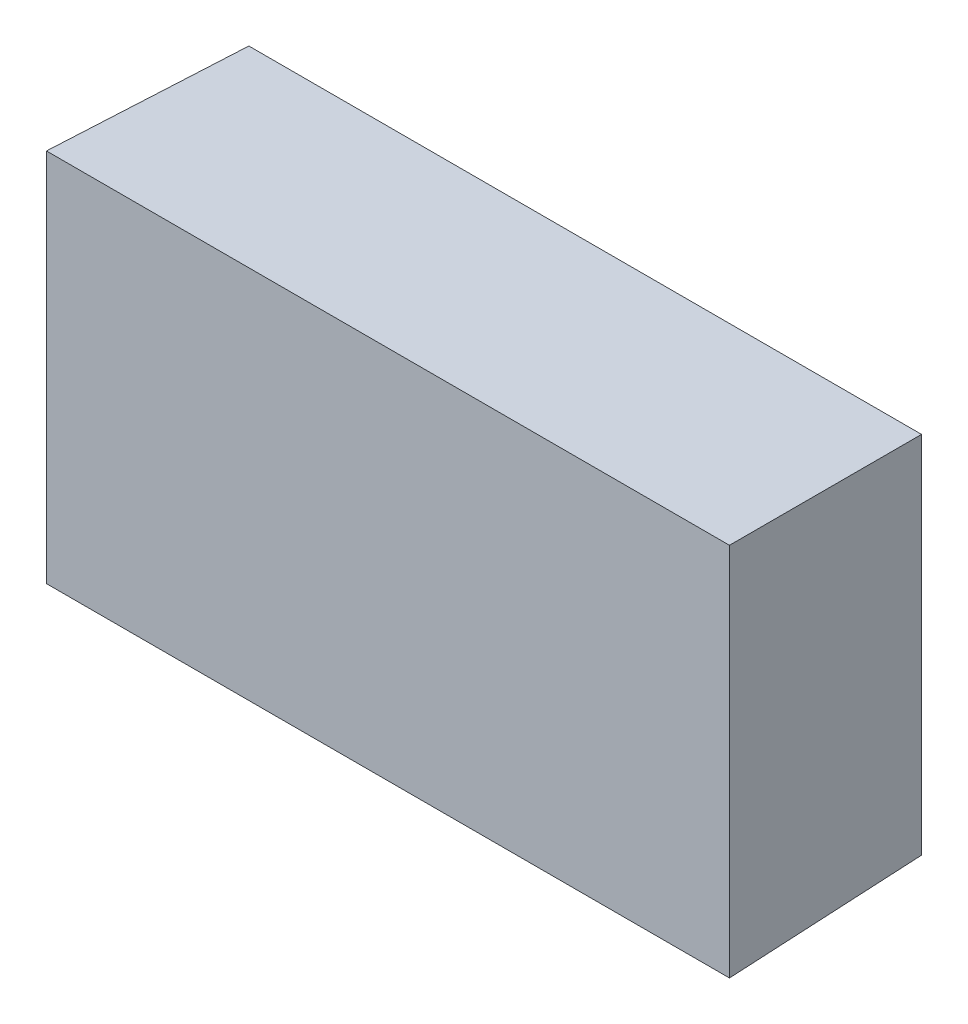
SolidWorks part; units mm, degrees
material "1060 Alloy"
ref_plane "Front Plane" through (0, 0, 0) normal (0, 0, 1) x (1, 0, 0)
ref_plane "Top Plane" through (0, 0, 0) normal (0, 1, 0) x (1, 0, 0)
ref_plane "Right Plane" through (0, 0, 0) normal (1, 0, 0) x (0, 0, -1)
sketch "Sketch1" plane through (0, 0, 0) normal (0, 0, 1) x (1, 0, 0)
  line L0 (60.6, 33.25) -> (-60.6, 33.25)
  line L1 (-60.6, 33.25) -> (-60.6, -33.25)
  line L2 (-60.6, -33.25) -> (60.6, -33.25)
  line L3 (60.6, -33.25) -> (60.6, 33.25)
  line L4 (0, -61.45) -> (0, -18.55) construction
  line L5 (-46.05, 0) -> (-88.95, 0) construction
  dimension "D1" = 121.2
  dimension "D2" = 66.5
  dimension "D3" = 60.6
  dimension "D4" = 33.25
extrude "Boss-Extrude1" add sketch "Sketch1" against normal blind 35 draft 1.5
sketch "Sketch2" plane through (0, 0, 0) normal (0, 0, 1) x (-1, 0, 0)
  line L0 (52.05, -24.5) -> (58.85, -24.5)
  line L1 (58.85, -24.5) -> (58.85, 24.5)
  line L2 (58.85, 24.5) -> (52.05, 24.5)
  line L3 (52.05, 24.5) -> (52.05, 31)
  line L4 (52.05, 31) -> (-52.05, 31)
  line L5 (-52.05, 31) -> (-52.05, 24.5)
  line L6 (-52.05, 24.5) -> (-58.85, 24.5)
  line L7 (-58.85, 24.5) -> (-58.85, -24.5)
  line L8 (-58.85, -24.5) -> (-52.05, -24.5)
  line L9 (-52.05, -24.5) -> (-52.05, -31)
  line L10 (-52.05, -31) -> (52.05, -31)
  line L11 (52.05, -31) -> (52.05, -24.5)
extrude "Cut-Extrude1" [suppressed] cut sketch "Sketch2" against normal blind 34.2 draft 1.5
fillet "Fillet1" [suppressed] radius 4.5
fillet "Fillet5" [suppressed] radius 1.5
fillet "Fillet9" [suppressed] radius 3.5
sketch "Sketch14" [suppressed] plane through (60.5585, 0, -1.5858) normal (0.9997, 0, -0.0262) x (-0.0262, 0.0003, -0.9997)
  line L0 (-1.596, -28.251) -> (-1.5766, 28.2521) construction
  circle A0 centre (17.2202, 22777.2454) radius 6.5
  circle A1 centre (-20.1573, -86279.8583) radius 6.5
  circle A2 centre (31.2702, 22761.2454) radius 5
  dimension "D3" = 13
  dimension "D6" = 13
  dimension "D9" = 10
  dimension "D1" = 11
  dimension "D2" = 18.7
  dimension "D4" = 11
  dimension "D5" = 18.7
  dimension "D7" = 16
  dimension "D8" = 32.75
extrude "Cut-Extrude5" [suppressed] cut sketch "Sketch14" against normal blind 3
sketch "Sketch15" [suppressed] plane through (0, 0, -35.8) normal (0, 0, -1) x (1, 0, 0)
  line L2 (-55.2023, -30.3513) -> (55.2023, -30.3513) construction
  line L3 (58.2013, -27.3523) -> (58.2013, 27.3523) construction
  line L4 (55.2023, 30.3513) -> (-55.2023, 30.3513) construction
  circle A0 centre (44.2013, 18.3513) radius 4.5
  circle A1 centre (44.2013, -18.3513) radius 4.5
  circle A2 centre (14.2013, 18.3513) radius 4.5
  circle A3 centre (14.2013, -18.3513) radius 4.5
  circle A4 centre (14.2013, 0.0013) radius 3.5
  dimension "D3" = 9
  dimension "D6" = 9
  dimension "D8" = 9
  dimension "D9" = 9
  dimension "D15" = 7
  dimension "D2" = 14
  dimension "D4" = 12
  dimension "D5" = 14
  dimension "D7" = 30
  dimension "D10" = 30
  dimension "D11" = 12
  dimension "D12" = 12
  dimension "D13" = 18.35
  dimension "D14" = 44
  dimension "D16" = 12
extrude "Cut-Extrude6" [suppressed] cut sketch "Sketch15" against normal blind 2
sketch "Sketch17" [suppressed] plane through (0, -35.8, 0) normal (0, -1, 0) x (1, 0, 0)
  line L2 (55.2023, 30.3513) -> (-55.2023, 30.3513) construction
  line L3 (-58.2013, 27.3523) -> (-58.2013, -27.3523) construction
  circle A0 centre (-48.2013, 0.0013) radius 6
  circle A1 centre (-48.2013, 16.0013) radius 2.75
  dimension "D1" = 12
  dimension "D5" = 5.5
  dimension "D2" = 30.35
  dimension "D3" = 10
  dimension "D4" = 16
  dimension "D6" = 10
extrude "Cut-Extrude7" [suppressed] cut sketch "Sketch17" against normal blind 2
